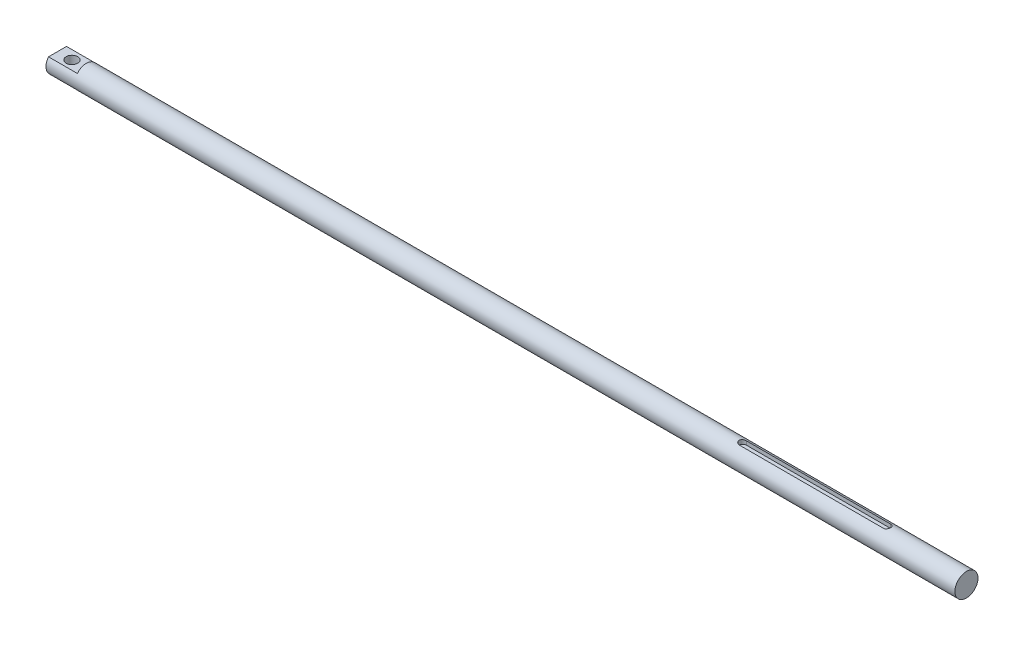
SolidWorks part; units mm, degrees
material "普通碳钢"
ref_plane "前视基准面" through (0, 0, 0) normal (0, 0, 1) x (1, 0, 0)
ref_plane "上视基准面" through (0, 0, 0) normal (0, 1, 0) x (1, 0, 0)
ref_plane "右视基准面" through (0, 0, 0) normal (1, 0, 0) x (0, 0, -1)
sketch "草图1" plane through (0, 0, 0) normal (1, 0, 0) x (0, 0, -1)
  circle A0 centre (0, 0) radius 8
  dimension "D1" = 16
extrude "凸台-拉伸1" add sketch "草图1" along normal blind 630
sketch "草图3" plane through (0, 0, 0) normal (-1, 0, 0) x (0, 0, 1)
  line L5 (-10, -5) -> (10, -5)
  line L6 (-10, -5) -> (-10, 5)
  line L7 (-10, 5) -> (10, 5)
  line L8 (10, -5) -> (10, 5)
  dimension "D1" = 10
  dimension "D2" = 5
  dimension "D3" = 20
  dimension "D4" = 10
sketch "草图2" plane through (0, 0, 0) normal (0, 1, 0) x (1, 0, 0)
  line L0 (0, 0) -> (630, 0) construction
  line L1 (630, -8) -> (630, 8) construction
  line L2 (0, 8) -> (0, -8) construction
  circle A0 centre (10, 0) radius 4
  dimension "D1" = 10
  dimension "D2" = 8
extrude "切除-拉伸1" cut sketch "草图2" against normal through all and the other way through all
extrude "切除-拉伸2" cut sketch "草图3" against normal blind 20 flip side to cut
sketch "草图4" plane through (0, 0, 0) normal (0, 1, 0) x (1, 0, 0)
  line L0 (475, 0) -> (575, 0) construction
  line L1 (475, 2.5) -> (575, 2.5)
  line L2 (475, -2.5) -> (575, -2.5)
  line L3 (0, 0) -> (475, 0) construction
  line L4 (630, -8) -> (630, 8) construction
  arc A0 (475, 2.5) -> (475, -2.5) centre (475, 0) ccw
  arc A1 (575, -2.5) -> (575, 2.5) centre (575, 0) ccw
  point P3 (525, 0)
  dimension "D1" = 105
  dimension "D2" = 100
  dimension "D3" = 5
ref_plane "基准面1" through (0, 5, 0) normal (0, 1, 0) x (1, 0, 0)
extrude "切除-拉伸3" cut sketch "草图4" along normal through all from surface at 5 starting at plane "基准面1"
